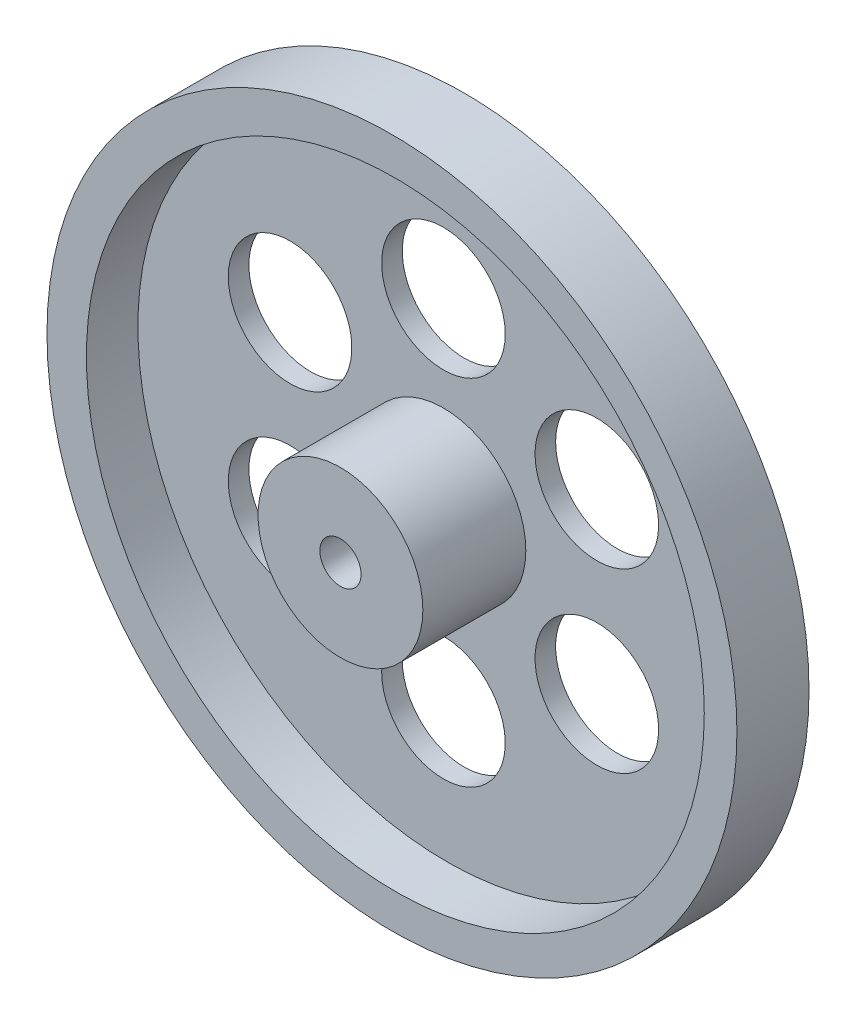
SolidWorks part; units mm, degrees
ref_plane "Front Plane" through (0, 0, 0) normal (0, 0, 1) x (1, 0, 0)
ref_plane "Top Plane" through (0, 0, 0) normal (0, 1, 0) x (1, 0, 0)
ref_plane "Right Plane" through (0, 0, 0) normal (1, 0, 0) x (0, 0, -1)
sketch "Sketch1" plane through (0, 0, 0) normal (0, 0, 1) x (1, 0, 0)
  circle A0 centre (0, 0) radius 33.5
  dimension "D1" = 67
extrude "Boss-Extrude1" add sketch "Sketch1" along normal blind 7
sketch "Sketch2" plane through (0, 0, 7) normal (0, 0, 1) x (1, 0, 0)
  circle A0 centre (0.3291, 0) radius 30
  dimension "D1" = 60
extrude "Cut-Extrude1" cut sketch "Sketch2" against normal blind 5
sketch "Sketch3" plane through (0, 0, 2) normal (0, 0, 1) x (1, 0, 0)
  circle A0 centre (0, 0) radius 8
  dimension "D1" = 16
extrude "Boss-Extrude2" add sketch "Sketch3" along normal blind 10
sketch "Sketch4" plane through (0, 0, 12) normal (0, 0, 1) x (1, 0, 0)
  circle A0 centre (0, 0) radius 2
extrude "Cut-Extrude2" cut sketch "Sketch4" against normal blind 30
sketch "Sketch5" plane through (0, 0, 2) normal (0, 0, 1) x (1, 0, 0)
  circle A0 centre (0, 17.1968) radius 6
extrude "Cut-Extrude3" cut sketch "Sketch5" against normal through all
pattern_circular "CirPattern1" count 6 over 360 about axis through (0, 0, 0) along (0, 0, 1) of "Cut-Extrude3"
